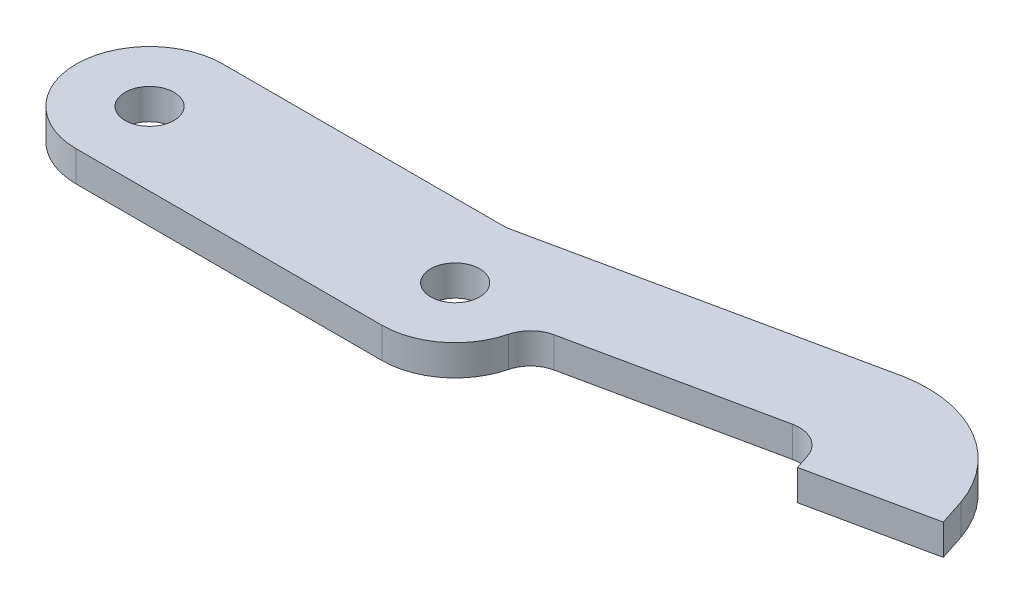
SolidWorks part; units mm, degrees
material "Epoxy, Unfilled"
ref_plane "Front Plane" through (0, 0, 0) normal (0, 0, 1) x (1, 0, 0)
ref_plane "Top Plane" through (0, 0, 0) normal (0, 1, 0) x (1, 0, 0)
ref_plane "Right Plane" through (0, 0, 0) normal (1, 0, 0) x (0, 0, -1)
sketch "Sketch1" plane through (0, 0, 0) normal (0, 1, 0) x (1, 0, 0)
  line L0 (0, 12) -> (46.3095, 12)
  line L3 (0, -12) -> (50, -12)
  line L4 (62, 0) -> (102, 8.5023)
  line L5 (46.3095, 12) -> (100.1077, 23.4351)
  line L6 (122.4396, 10.3048) -> (123.8266, 6.0238)
  line L7 (146.0527, 1.8431) -> (104.1576, 1.8431) construction
  line L8 (104.1576, 1.8431) -> (102, 8.5023)
  line L9 (50, 0) -> (91.7136, 0) construction
  line L10 (104.1576, 1.8431) -> (123.8266, 6.0238)
  circle A0 centre (0, 0) radius 4
  circle A1 centre (50, 0) radius 4
  arc A2 (0, 12) -> (0, -12) centre (0, 0) ccw
  arc A3 (50, -12) -> (62, 0) centre (50, 0) ccw
  arc A5 (122.4396, 10.3048) -> (100.1077, 23.4351) centre (103.5499, 3.7336) ccw
  dimension "D1" = 8
  dimension "D2" = 24
  dimension "D10" = 20
  dimension "D3" = 50
  dimension "D4" = 15
  dimension "D5" = 4.5
  dimension "D6" = 20
  dimension "D7" = 40
  dimension "D8" = 12
  dimension "D9" = 12
  dimension "D11" = 55
  dimension "D12" = 7
extrude "Boss-Extrude1" add sketch "Sketch1" along normal blind 5
fillet "Fillet1" radius 5 3 edges at (62, 2.5, 0) (102, 2.5, -8.5023) (46.3095, 2.5, -12)
scale "Scale1" scale about centroid uniform scaling yes scale factor 0.5
